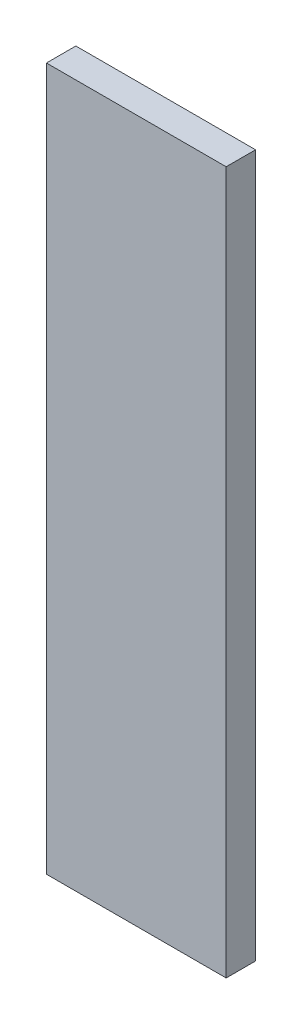
SolidWorks part; units mm, degrees
material "Balsa"
ref_plane "Front Plane" through (0, 0, 0) normal (0, 0, 1) x (1, 0, 0)
ref_plane "Top Plane" through (0, 0, 0) normal (0, 1, 0) x (1, 0, 0)
ref_plane "Right Plane" through (0, 0, 0) normal (1, 0, 0) x (0, 0, -1)
sketch "Sketch1" plane through (0, 0, 0) normal (0, 0, 1) x (1, 0, 0)
  line L1 (-55, 215) -> (55, 215)
  line L2 (-55, 215) -> (-55, -215)
  line L3 (-55, -215) -> (55, -215)
  line L4 (55, 215) -> (55, -215)
  line L5 (-55, 215) -> (55, -215) construction
  line L6 (-55, -215) -> (55, 215) construction
  point P0 (0, 0)
  dimension "D1" = 110
  dimension "D2" = 430
extrude "Boss-Extrude1" add sketch "Sketch1" along normal blind 18
